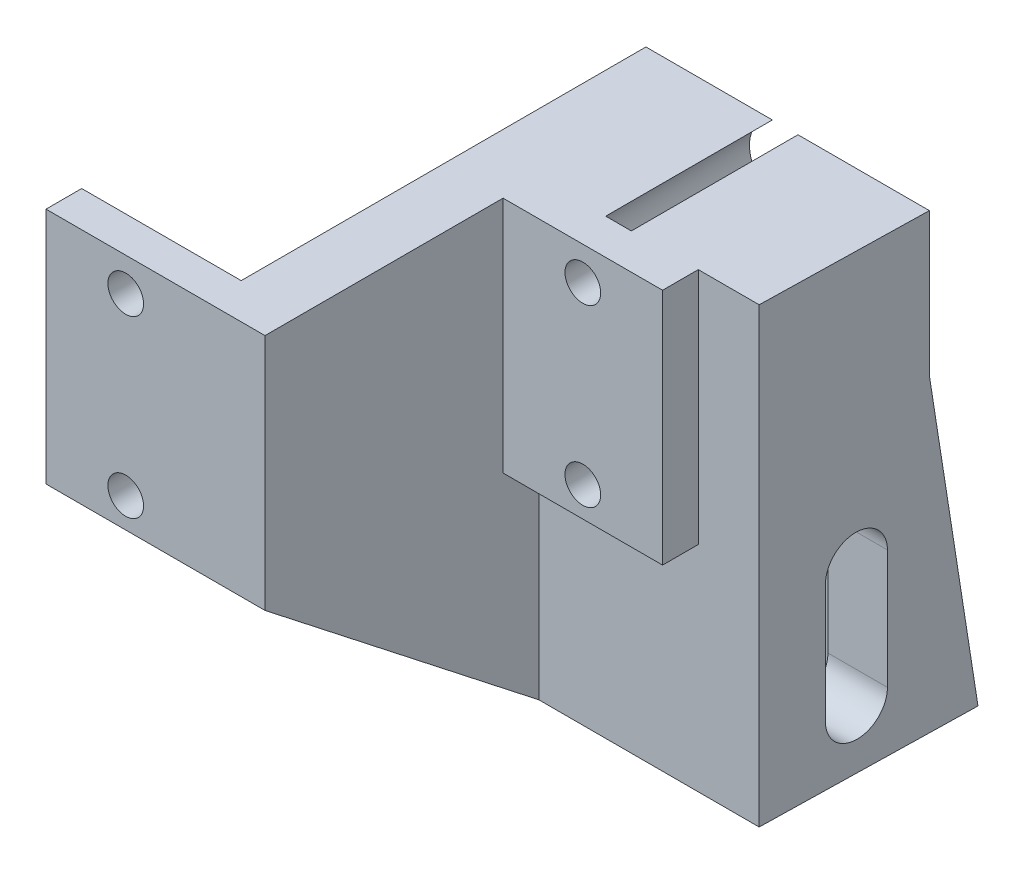
SolidWorks part; units mm, degrees
ref_plane "Front Plane" through (0, 0, 0) normal (0, 0, 1) x (1, 0, 0)
ref_plane "Top Plane" through (0, 0, 0) normal (0, 1, 0) x (1, 0, 0)
ref_plane "Right Plane" through (0, 0, 0) normal (1, 0, 0) x (0, 0, -1)
sketch "Sketch1" plane through (0, 0, 0) normal (0, 1, 0) x (1, 0, 0)
  line L0 (0, 0) -> (18.4, 0)
  line L1 (18.4, 0) -> (18.4, 20)
  line L2 (18.4, 20) -> (31.8, 20)
  line L3 (31.8, 20) -> (31.8, 23)
  line L4 (31.8, 23) -> (13.4, 23)
  line L5 (13.4, 23) -> (13.4, 3)
  line L6 (13.4, 3) -> (0, 3)
  line L7 (0, 3) -> (0, 0)
  dimension "D1" = 13.4
  dimension "D2" = 5
  dimension "D3" = 3
  dimension "D4" = 17
extrude "Boss-Extrude1" add sketch "Sketch1" along normal blind 20
sketch "Sketch2" plane through (0, 0, -20) normal (0, 0, 1) x (1, 0, 0)
  line L0 (25.1, 20) -> (25.1, 0) construction
  line L2 (31.8, 0) -> (13.4, 0) construction
  line L3 (18.4, 20) -> (31.8, 20) construction
  line L4 (18.4, 0) -> (31.8, 0) construction
  circle A0 centre (25.1, 2.5) radius 1.5
  circle A1 centre (25.1, 17.2) radius 1.5
  dimension "D1" = 3
  dimension "D2" = 2.5
  dimension "D3" = 14.7
extrude "Cut-Extrude1" cut sketch "Sketch2" against normal through all both and the other way through all
ref_plane "Plane1" through (15.9, 0, 0) normal (-1, 0, 0) x (0, 0, 1)
mirror "Mirror1" about plane through (15.9, 0, 0) normal (-1, 0, 0) of "Cut-Extrude1"
sketch "Sketch3" plane through (13.4, 0, 0) normal (-1, 0, 0) x (0, 0, 1)
  line L0 (-23, 0) -> (-23, -18)
  line L1 (-23, -18) -> (-41, -18)
  line L2 (-41, -18) -> (-37, 8)
  line L3 (-37, 8) -> (-37, 20)
  line L4 (-37, 20) -> (-23, 20)
  line L5 (-23, 20) -> (-23, 0)
  line L6 (-23, 0) -> (-3, 0) construction
  line L7 (-31, -13) -> (-31, -3) construction
  line L8 (-33.55, -13) -> (-33.55, -3)
  line L9 (-28.45, -13) -> (-28.45, -3)
  arc A0 (-33.55, -13) -> (-28.45, -13) centre (-31, -13) ccw
  arc A1 (-28.45, -3) -> (-33.55, -3) centre (-31, -3) ccw
  point P12 (-31, -8)
  dimension "D1" = 18
  dimension "D2" = 14
  dimension "D3" = 12
  dimension "D4" = 18
  dimension "D5" = 5.1
  dimension "D6" = 10
  dimension "D7" = 5
  dimension "D8" = 8
extrude "Boss-Extrude2" add sketch "Sketch3" against normal offset from surface (23.9 mm away) 5.5 up to face at (31.8, 10, -21.5) offset beyond the face yes
sketch "Sketch4" plane through (0, 0, -23) normal (0, 0, 1) x (1, 0, 0)
  circle A0 centre (25.1, 2.5) radius 3
  circle A1 centre (25.1, 17.2) radius 3
  dimension "D1" = 6
extrude "Cut-Extrude2" cut sketch "Sketch4" against normal through all
sketch "Sketch5" plane through (13.4, 0, 0) normal (-1, 0, 0) x (0, 0, 1)
  line L0 (0, 0) -> (-23, -18)
  line L1 (-23, -18) -> (-23, 0)
  line L2 (-23, 0) -> (0, 0)
extrude "Boss-Extrude3" add sketch "Sketch5" against normal up to surface (5 mm away) up to face at (18.4, 10, -10)
sketch "Sketch8" plane through (0, -18, 0) normal (0, -1, 0) x (1, 0, 0)
  line L0 (37.3, -41) -> (36.9167, -23)
  line L1 (37.3, -23) -> (18.4, -23) construction
  line L2 (36.9167, -23) -> (37.3, -23)
  line L3 (37.3, -23) -> (37.3, -41)
  dimension "D1" = 1.22
extrude "Cut-Extrude3" cut sketch "Sketch8" against normal through all
sketch "Sketch9" plane through (13.4, 0, 0) normal (-1, 0, 0) x (0, 0, 1)
  line L0 (-37, -3) -> (-37, -18)
  line L3 (-25, -3) -> (-25, -18)
  line L4 (-41, -18) -> (-23, -18) construction
  line L5 (-37, -18) -> (-25, -18)
  arc A4 (-37, -3) -> (-25, -3) centre (-31, -3) cw
  arc A5 (-28.45, -3) -> (-33.55, -3) centre (-31, -3) ccw construction
  dimension "D1" = 6
extrude "Cut-Extrude4" cut sketch "Sketch9" against normal offset from surface (18.8137 mm away) 5
